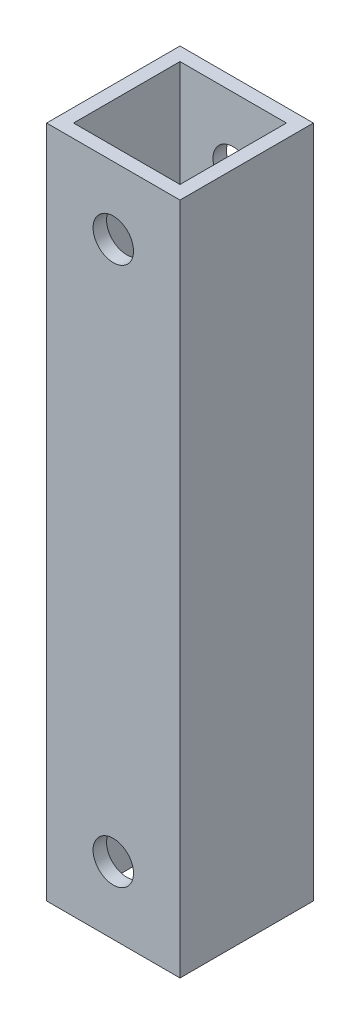
SolidWorks part; units mm, degrees
ref_plane "Спереди" through (0, 0, 0) normal (0, 0, 1) x (1, 0, 0)
ref_plane "Сверху" through (0, 0, 0) normal (0, 1, 0) x (1, 0, 0)
ref_plane "Справа" through (0, 0, 0) normal (1, 0, 0) x (0, 0, -1)
sketch "Эскиз1" plane through (0, 0, 0) normal (0, 1, 0) x (1, 0, 0)
  line L0 (-4.95, -4.95) -> (4.95, 4.95) construction
  line L1 (4.95, -4.95) -> (-4.95, -4.95)
  line L2 (4.95, -4.95) -> (4.95, 4.95)
  line L3 (4.95, 4.95) -> (-4.95, 4.95)
  line L4 (-4.95, -4.95) -> (-4.95, 4.95)
  line L6 (3.95, 3.95) -> (-3.95, 3.95)
  line L7 (3.95, 3.95) -> (3.95, -3.95)
  line L8 (3.95, -3.95) -> (-3.95, -3.95)
  line L9 (-3.95, 3.95) -> (-3.95, -3.95)
  line L10 (3.95, 3.95) -> (-3.95, -3.95) construction
  line L11 (3.95, -3.95) -> (-3.95, 3.95) construction
  point P0 (0, 0)
  point P6 (0, 0)
  point P7 (0, 0)
  point P12 (0, 0)
  point P13 (0, 0)
  point P14 (0, 0)
  dimension "D1" = 1
  dimension "D2" = 9.9
extrude "Бобышка-Вытянуть1" add sketch "Эскиз1" along normal blind 50
sketch "Sketch2" plane through (0, 0, -4.95) normal (0, 0, -1) x (-1, 0, 0)
  line L0 (0, 50) -> (0, 0) construction
  line L1 (-4.95, 50) -> (4.95, 50) construction
  line L2 (-4.95, 0) -> (4.95, 0) construction
  circle A0 centre (0, 45) radius 1.5
  circle A1 centre (0, 5) radius 1.5
  dimension "D2" = 3
  dimension "D3" = 40
  dimension "D1" = 5
extrude "Cut-Extrude2" cut sketch "Sketch2" against normal through all
